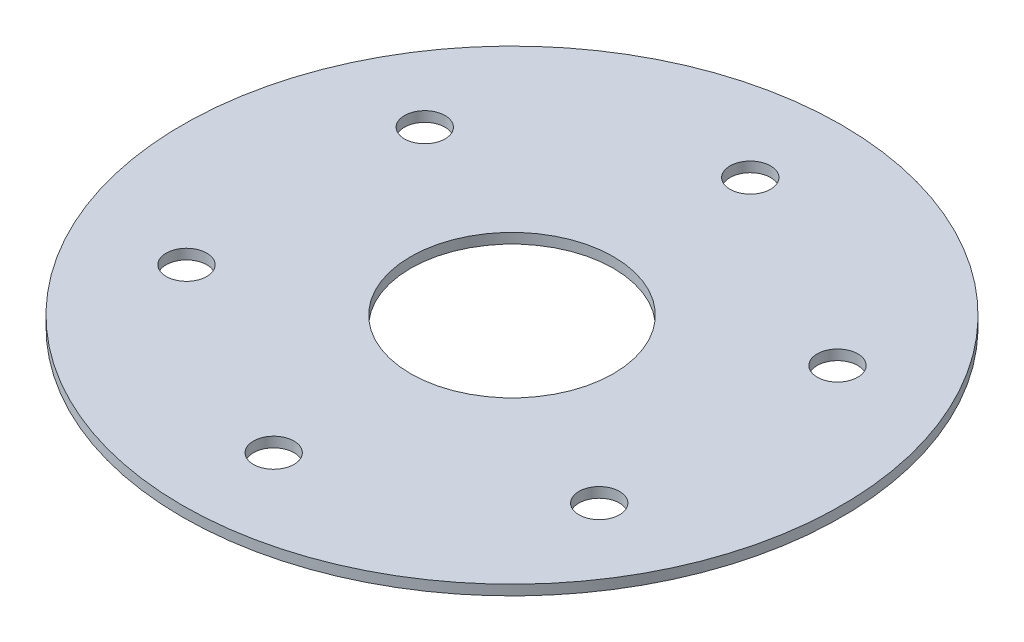
SolidWorks part; units mm, degrees
ref_plane "Front Plane" through (0, 0, 0) normal (0, 0, 1) x (1, 0, 0)
ref_plane "Top Plane" through (0, 0, 0) normal (0, 1, 0) x (1, 0, 0)
ref_plane "Right Plane" through (0, 0, 0) normal (1, 0, 0) x (0, 0, -1)
sketch "Sketch1" plane through (0, 0, 0) normal (0, 1, 0) x (1, 0, 0)
  line L0 (0, 0) -> (0, 30.3456) construction
  circle A0 centre (0, 0) radius 32.5
  circle A1 centre (0, 0) radius 10
  circle A2 centre (0, 0) radius 23.5 construction
  circle A3 centre (0, 23.5) radius 2
  circle A4 centre (20.3516, 11.75) radius 2
  circle A5 centre (20.3516, -11.75) radius 2
  circle A6 centre (0, -23.5) radius 2
  circle A7 centre (-20.3516, -11.75) radius 2
  circle A8 centre (-20.3516, 11.75) radius 2
  point P20 (0, 0)
  dimension "D1" = 65
  dimension "D2" = 47
  dimension "D3" = 20
  dimension "D4" = 4
  dimension "D5" = 6
extrude "Boss-Extrude1" add sketch "Sketch1" along normal blind 1
